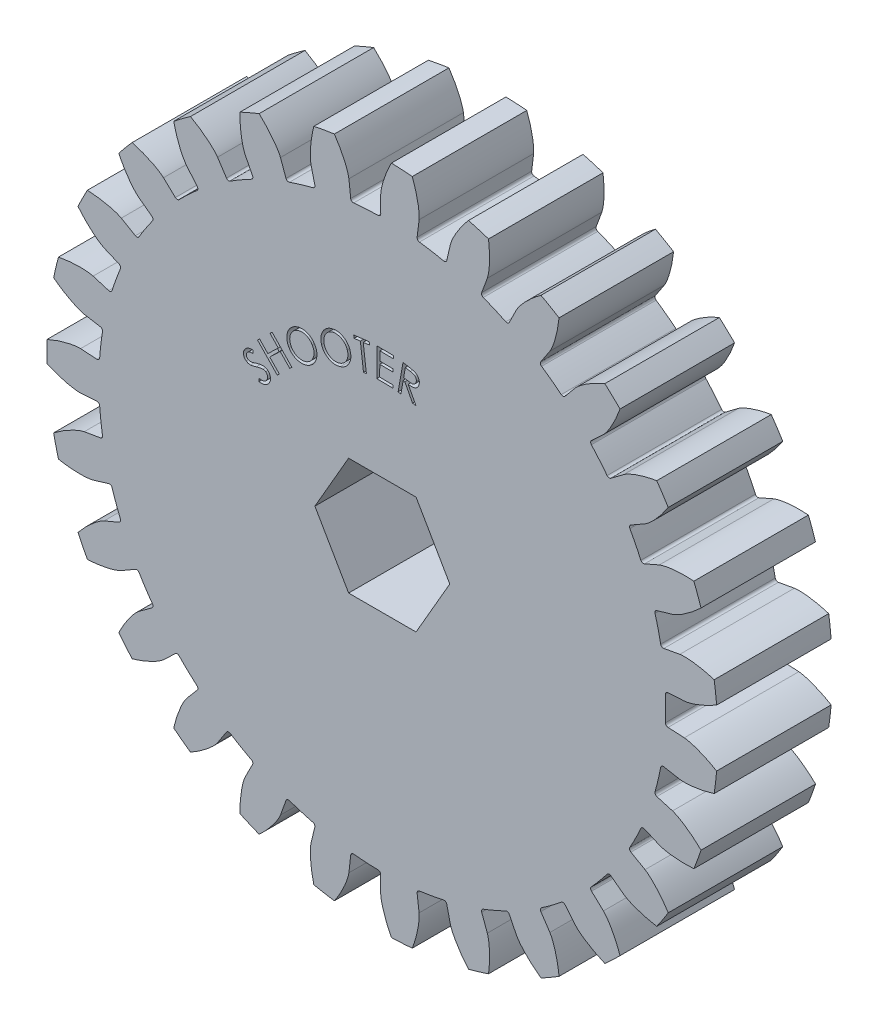
SolidWorks part; units mm, degrees
ref_plane "Front Plane" through (0, 0, 0) normal (0, 0, 1) x (1, 0, 0)
ref_plane "Top Plane" through (0, 0, 0) normal (0, 1, 0) x (1, 0, 0)
ref_plane "Right Plane" through (0, 0, 0) normal (1, 0, 0) x (0, 0, -1)
sketch "Sketch1" plane through (0, 0, 0) normal (0, 0, 1) x (1, 0, 0)
  circle A0 centre (0, 0) radius 37.202
extrude "BodyBlank" add sketch "Sketch1" along normal blind 12.7
ref_plane "CirclesPlane" through (0, 0, 12.7) normal (0, 0, 1) x (1, 0, 0)
sketch "EqDrivenInvoluteCurves" plane through (0, 0, 12.7) normal (0, 0, 1) x (1, 0, 0)
  line L0 (0, 0) -> (31.3858, 1.6534) construction
  line L1 (31.3858, -1.6534) -> (0, 0) construction
  line L2 (31.6816, 1.669) -> (33.4867, 1.7641)
  line L3 (31.6816, -1.669) -> (33.4867, -1.7641)
  circle A0 centre (0, 0) radius 31.4293 construction
  circle A1 centre (0, 0) radius 33.5331 construction
  circle A2 centre (0, 0) radius 34.6364 construction
  circle A3 centre (0, 0) radius 37.202 construction
  arc A4 (37.0671, 3.1654) -> (37.0671, -3.1654) centre (0, 0) cw
  arc A5 (31.3999, 1.3589) -> (31.3999, -1.3589) centre (0, 0) cw
  arc A6 (31.6816, 1.669) -> (31.3999, 1.3589) centre (31.6973, 1.3718) ccw
  arc A7 (31.3999, -1.3589) -> (31.6816, -1.669) centre (31.6973, -1.3718) ccw
  spline S0 degree 4 poles (33.4867, 1.7641) (33.4924, 1.7645) (33.5084, 1.7657) (33.5386, 1.7686) (33.5879, 1.7745) (33.6505, 1.7834) (33.7314, 1.7966) (33.8266, 1.8144) (33.931, 1.8362) (34.0444, 1.8624) (34.1574, 1.8908) (34.2699, 1.9211) (34.3818, 1.9531) (34.5172, 1.9941) (34.6793, 2.0463) (34.8683, 2.1117) (35.0821, 2.1911) (35.2995, 2.2776) (35.5129, 2.3673) (35.7279, 2.4632) (35.9356, 2.5597) (36.1506, 2.6653) (36.3488, 2.7655) (36.5701, 2.8838) (36.7485, 2.981) (36.983, 3.1156) (37.1213, 3.197) (37.2829, 3.2945) (37.3545, 3.3389) (37.3986, 3.3663) knots 0 0 0 0 0 0.005377 0.015084 0.028532 0.04661 0.064855 0.092111 0.119476 0.146842 0.174209 0.201575 0.228941 0.256307 0.307035 0.361767 0.4165 0.471232 0.525964 0.580697 0.635429 0.690161 0.744894 0.799626 0.854358 0.909091 0.954545 1 1 1 1 1 construction
  spline S1 degree 4 poles (33.4867, 1.7641) (33.4924, 1.7645) (33.5084, 1.7657) (33.5386, 1.7686) (33.5879, 1.7745) (33.6505, 1.7834) (33.7314, 1.7966) (33.8266, 1.8144) (33.931, 1.8362) (34.0444, 1.8624) (34.1574, 1.8908) (34.2699, 1.9211) (34.3818, 1.9531) (34.5172, 1.9941) (34.6793, 2.0463) (34.8683, 2.1117) (35.0821, 2.1911) (35.2995, 2.2776) (35.5129, 2.3673) (35.7279, 2.4632) (35.9356, 2.5597) (36.1506, 2.6653) (36.3488, 2.7655) (36.5701, 2.8838) (36.7485, 2.981) (36.9322, 3.0864) (37.0215, 3.1385) (37.0671, 3.1654) knots 0 0 0 0 0 0.005377 0.015084 0.028532 0.04661 0.064855 0.092111 0.119476 0.146842 0.174209 0.201575 0.228941 0.256307 0.307035 0.361767 0.4165 0.471232 0.525964 0.580697 0.635429 0.690161 0.744894 0.799626 0.854358 0.909091 0.909091 0.909091 0.909091 0.909091
  spline S2 degree 4 poles (33.4867, -1.7641) (33.4924, -1.7645) (33.5084, -1.7657) (33.5386, -1.7686) (33.5879, -1.7745) (33.6505, -1.7834) (33.7314, -1.7966) (33.8266, -1.8144) (33.931, -1.8362) (34.0444, -1.8624) (34.1574, -1.8908) (34.2699, -1.9211) (34.3818, -1.9531) (34.5172, -1.9941) (34.6793, -2.0463) (34.8683, -2.1117) (35.0821, -2.1911) (35.2995, -2.2776) (35.5129, -2.3673) (35.7279, -2.4632) (35.9356, -2.5597) (36.1506, -2.6653) (36.3488, -2.7655) (36.5701, -2.8838) (36.7485, -2.981) (36.983, -3.1156) (37.1213, -3.197) (37.2829, -3.2945) (37.3545, -3.3389) (37.3986, -3.3663) knots 0 0 0 0 0 0.005377 0.015084 0.028532 0.04661 0.064855 0.092111 0.119476 0.146842 0.174209 0.201575 0.228941 0.256307 0.307035 0.361767 0.4165 0.471232 0.525964 0.580697 0.635429 0.690161 0.744894 0.799626 0.854358 0.909091 0.954545 1 1 1 1 1 construction
  spline S3 degree 4 poles (33.4867, -1.7641) (33.4924, -1.7645) (33.5084, -1.7657) (33.5386, -1.7686) (33.5879, -1.7745) (33.6505, -1.7834) (33.7314, -1.7966) (33.8266, -1.8144) (33.931, -1.8362) (34.0444, -1.8624) (34.1574, -1.8908) (34.2699, -1.9211) (34.3818, -1.9531) (34.5172, -1.9941) (34.6793, -2.0463) (34.8683, -2.1117) (35.0821, -2.1911) (35.2995, -2.2776) (35.5129, -2.3673) (35.7279, -2.4632) (35.9356, -2.5597) (36.1506, -2.6653) (36.3488, -2.7655) (36.5701, -2.8838) (36.7485, -2.981) (36.9322, -3.0864) (37.0215, -3.1385) (37.0671, -3.1654) knots 0 0 0 0 0 0.005377 0.015084 0.028532 0.04661 0.064855 0.092111 0.119476 0.146842 0.174209 0.201575 0.228941 0.256307 0.307035 0.361767 0.4165 0.471232 0.525964 0.580697 0.635429 0.690161 0.744894 0.799626 0.854358 0.909091 0.909091 0.909091 0.909091 0.909091
  dimension "D5" = 0.2977
extrude "ToothCutMaster" cut sketch "EqDrivenInvoluteCurves" against normal through all
pattern_circular "ToothCutsPattern" count 27 over 360 about axis through (0, 0, 12.7) along (0, 0, -1) of "ToothCutMaster"
sketch "Sketch2" plane through (0, 0, 12.7) normal (0, 0, 1) x (1, 0, 0)
  line L1 (3.7395, 6.477) -> (-3.7395, 6.477)
  line L2 (-3.7395, 6.477) -> (-7.479, 0)
  line L3 (-7.479, 0) -> (-3.7395, -6.477)
  line L4 (-3.7395, -6.477) -> (3.7395, -6.477)
  line L5 (3.7395, -6.477) -> (7.479, 0)
  line L6 (7.479, 0) -> (3.7395, 6.477)
  circle A0 centre (0, 0) radius 6.477 construction
  dimension "D1" = 12.954
extrude "Cut-Extrude1" cut sketch "Sketch2" against normal through all
sketch "Sketch3" plane through (0, 0, 12.7) normal (0, 0, 1) x (1, 0, 0)
  line L0 (0, 0) -> (-1.8275, 31.3761) construction
  arc A0 (-13.2364, 8.4704) -> (12.1636, 9.9498) centre (0, 0) cw construction
  arc A1 (-0.4691, 31.4258) -> (-3.1824, 31.2678) centre (0, 0) ccw construction
  text T0 "SHOOTER"
  point P5 (-0.9137, 15.6881)
  dimension "D1" = 25.4
extrude "Shooter" cut sketch "Sketch3" against normal blind 1.27
equation "\"DiametralPitch\"= 9.9"
equation "\"NumTeeth\"= 27"
equation "\"FaceWidth\"= .5"
equation "\"PressureAngle\"= 14.5deg"
equation "\"Addendum\"= 1 / \"DiametralPitch\""
equation "\"Dedendum\"= 1.25 / \"DiametralPitch\""
equation "\"WorkingDepth\"= 2 / \"DiametralPitch\""
equation "\"WholeDepth\"= 2.25 / \"DiametralPitch\""
equation "\"Clearance\"= 0.25 / \"DiametralPitch\""
equation "\"ToothThickness\"= 1.5708 / \"DiametralPitch\""
equation "\"CircularPitch\"= pi / \"DiametralPitch\""
equation "\"PitchCircle\"= \"NumTeeth\" / \"DiametralPitch\""
equation "\"OutsideDiameter\"= ( \"NumTeeth\" + 2 ) / \"DiametralPitch\""
equation "\"Fillet\"= \"Clearance\" * cos ( \"PressureAngle\" ) * tan ( ( 90 + \"PressureAngle\" ) / 2 )"
equation "\"AddendumCircle\"= \"PitchCircle\" + ( 2 * \"Addendum\" )"
equation "\"DedendumCircle\"= \"PitchCircle\" - ( 2 * \"Dedendum\" )"
equation "\"BaseCircle\"= \"PitchCircle\" * cos ( \"PressureAngle\" )"
equation "\"PitchAngle\"= 360deg / \"NumTeeth\""
equation "\"Alpha\"= sqr ( \"PitchCircle\" ^ 2 - \"BaseCircle\" ^ 2 ) / \"BaseCircle\" * 180 / PI - \"PressureAngle\""
equation "\"Beta\"= ( \"PitchAngle\" / 4 - \"Alpha\" )"
equation "\"Phi\"= sqr ( ( \"AddendumCircle\" / 2 ) ^ 2 - ( \"BaseCircle\" / 2 ) ^ 2 ) / ( \"BaseCircle\" / 2 )"
equation "\"D1@Sketch1\"=\"OutsideDiameter\""
equation "\"D1@BodyBlank\" = \"FaceWidth\""
equation "\"D1@EqDrivenInvoluteCurves\" = \"OutsideDiameter\""
equation "\"D2@EqDrivenInvoluteCurves\" = \"PitchCircle\""
equation "\"D3@EqDrivenInvoluteCurves\" = \"BaseCircle\""
equation "\"D4@EqDrivenInvoluteCurves\" = \"DedendumCircle\""
equation "\"D1@ToothCutsPattern\"=\"NumTeeth\""
